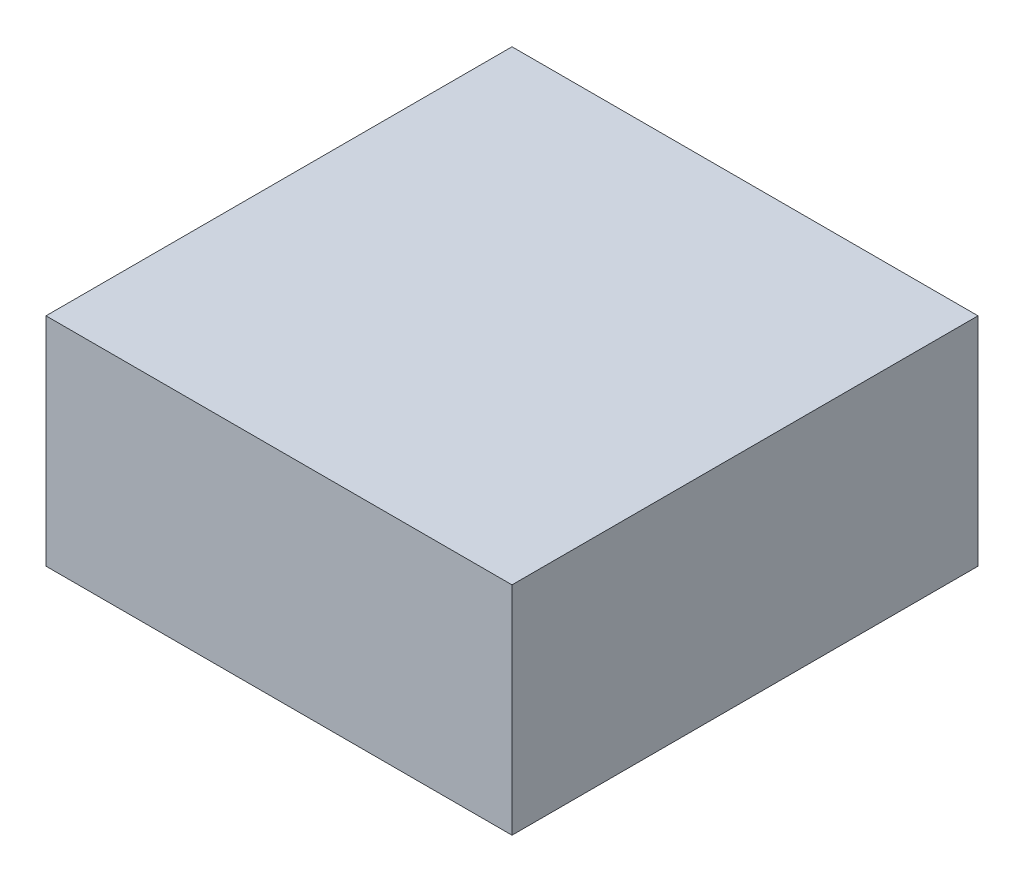
SolidWorks part; units mm, degrees
ref_plane "Front Plane" through (0, 0, 0) normal (0, 0, 1) x (1, 0, 0)
ref_plane "Top Plane" through (0, 0, 0) normal (0, 1, 0) x (1, 0, 0)
ref_plane "Right Plane" through (0, 0, 0) normal (1, 0, 0) x (0, 0, -1)
sketch "Sketch1" plane through (0, 0, 0) normal (0, 1, 0) x (1, 0, 0)
  line L1 (-25.25, -25.25) -> (25.25, -25.25)
  line L2 (-25.25, -25.25) -> (-25.25, 25.25)
  line L3 (-25.25, 25.25) -> (25.25, 25.25)
  line L4 (25.25, -25.25) -> (25.25, 25.25)
  line L5 (-25.25, -25.25) -> (25.25, 25.25) construction
  line L6 (-25.25, 25.25) -> (25.25, -25.25) construction
  point P0 (0, 0)
  dimension "D1" = 50.5
  dimension "D2" = 50.5
extrude "Boss-Extrude1" add sketch "Sketch1" along normal blind 23.5
sketch "Sketch2" plane through (0, 23.5, 0) normal (0, 1, 0) x (1, 0, 0)
  text T0 "Control" font "Century Gothic" height in points 36
